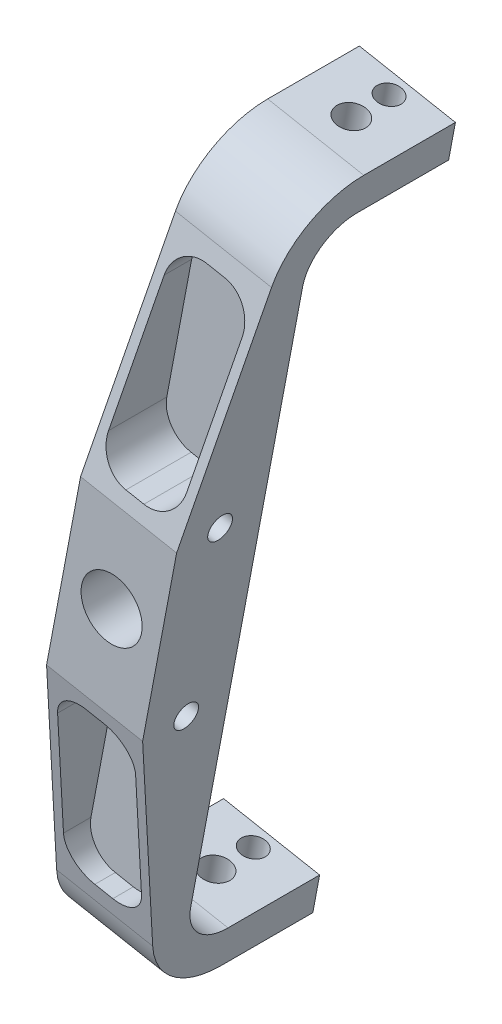
SolidWorks part; units mm, degrees
other "Markup1"
sketch "Sketch6" plane through (39.3536, 123.4271, -45) normal (0.998, 0.0328, -0.0532) x (-0.0595, 0.2351, -0.9701)
other "Markup2"
sketch "Sketch7" plane through (39.3536, 123.4271, -45) normal (0.9999, 0.0057, -0.0131) x (0.0031, -0.9818, -0.1901)
other "Markup4"
sketch "Sketch9" plane through (-39.3536, 123.4271, 27) normal (-0.9915, 0.1233, 0.0413) x (-0.1205, -0.9906, 0.0646)
other "Markup5"
sketch "Sketch12" plane through (-39.3536, 123.4271, 28.5) normal (-0.7749, 0.0474, 0.6304) x (0.632, 0.0395, 0.7739)
material "6061-T6 (SS)"
ref_plane "Front Plane" through (0, 0, 0) normal (0, 0, 1) x (1, 0, 0)
ref_plane "Top Plane" through (0, 0, 0) normal (0, 1, 0) x (1, 0, 0)
ref_plane "Right Plane" through (0, 0, 0) normal (1, 0, 0) x (0, 0, -1)
sketch "Sketch1" plane through (0, 0, 0) normal (0, 0, 1) x (1, 0, 0)
  line L0 (23.3397, 123.7002) -> (23.3397, 145.9252) construction
  line L1 (0, 0) -> (0, -276.86) construction
  line L2 (0, -276.86) -> (-52.2377, -276.86) construction
  line L3 (23.3397, 123.7002) -> (-52.2377, -276.86) construction
  line L8 (-23.3397, -123.7002) -> (-27.4603, -145.5398) construction
  line L9 (-7.6171, -126.6667) -> (39.0622, 120.7336)
  line L14 (-39.0622, -120.7336) -> (7.6171, 126.6667)
  line L17 (23.3397, 123.7002) -> (27.4603, 145.5398) construction
  line L19 (-7.6171, -126.6667) -> (-39.0622, -120.7336)
  line L20 (-23.3397, -123.7002) -> (-25.4, -134.62) construction
  line L21 (7.6171, 126.6667) -> (39.0622, 120.7336)
  line L22 (23.3397, 123.7002) -> (-23.3397, -123.7002) construction
  circle A0 centre (0, 0) radius 276.86 construction
  circle A1 centre (0, 0) radius 10
  circle A2 centre (0, 0) radius 170.5 construction
  point P4 (25.4, 134.62)
  point P6 (0, 0)
  point P10 (0, -170.5)
  point P13 (-10.5081, -129.9032)
  point P17 (0, 0)
  point P18 (41.7595, 124.248)
  point P19 (-41.8145, -123.9803)
  point P20 (10.5081, 129.9032)
  point P25 (-25.4, -134.62)
  point P31 (0, 0)
  point P32 (-23.3397, -123.7002)
  dimension "D4" = 341
  dimension "D9" = 20
  dimension "D2" = 553.72
  dimension "D3" = 22.225
  dimension "D5" = 50.8
  dimension "D6" = 32
  dimension "D7" = 52.2377
  dimension "D8" = 251.7655
  dimension "D11" = 11.1125
  dimension "D12" = 269.24
extrude "Boss-Extrude1" add sketch "Sketch1" along normal blind 28.5
sketch "Sketch2" plane through (0, 0, 0) normal (0, 0, -1) x (-1, 0, 0)
  line L0 (-36.8373, 108.9417) -> (-5.3922, 114.8748)
  line L1 (5.3922, -114.8748) -> (36.8373, -108.9417)
  line L2 (-5.3922, 114.8748) -> (-7.6171, 126.6667)
  line L3 (5.3922, -114.8748) -> (7.6171, -126.6667)
  line L4 (-7.6171, 126.6667) -> (-39.0622, 120.7336)
  line L5 (-39.0622, 120.7336) -> (7.6171, -126.6667)
  line L6 (-7.6171, 126.6667) -> (-39.0622, 120.7336)
  line L7 (39.0622, -120.7336) -> (-7.6171, 126.6667)
  line L9 (-39.0622, 120.7336) -> (-36.8373, 108.9417)
  line L11 (39.0622, -120.7336) -> (36.8373, -108.9417)
  line L14 (7.6171, -126.6667) -> (39.0622, -120.7336)
  line L15 (7.6171, -126.6667) -> (39.0622, -120.7336)
  dimension "D2" = 12
  dimension "D1" = 0
extrude "Boss-Extrude2" add sketch "Sketch2" along normal blind 45
sketch "Sketch4" plane through (-1.6562, 128.4164, 0) normal (0.1854, 0.9827, 0) x (0.9827, -0.1854, 0)
  line L0 (25.4368, -28.5) -> (25.4368, 45) construction
  line L3 (9.4368, 45) -> (41.4368, 45) construction
  line L12 (9.4368, 26.6476) -> (41.4368, 26.6476) construction
  line L13 (9.4368, -28.5) -> (9.4368, 45) construction
  line L14 (41.4368, -28.5) -> (41.4368, 45) construction
  circle A0 centre (25.4368, 26.6476) radius 4.7625
  circle A1 centre (25.4368, 39) radius 3.9688
  point P6 (25.4368, 26.6476)
  dimension "D2" = 9.525
  dimension "D3" = 7.9375
  dimension "D1" = 18.3524
  dimension "D4" = 6
extrude "Cut-Extrude1" cut sketch "Sketch4" against normal through all
fillet "Fillet3" radius 15 2 edges at (21.1148, 111.9082, 0) (-21.1148, -111.9082, 0)
sketch "Sketch10" plane through (-16.0243, 1.3676, 0) normal (0.9827, -0.1854, 0) x (0, 0, -1)
  line L0 (-28.5, 31.6271) -> (-11.3167, 106.5459)
  line L1 (-28.5, 31.6271) -> (-46.9127, 31.4169)
  line L2 (-46.9127, 31.4169) -> (-44.7685, 140.1716)
  line L3 (-44.7685, 140.1716) -> (15, 127.5099)
  line L4 (0, 1.6271) -> (-52.8517, 1.6271) construction
  line L5 (-28.5, 127.5099) -> (45, 127.5099) construction
  line L6 (-28.5, -124.2556) -> (-28.5, 127.5099) construction
  line L7 (-44.7685, -136.9173) -> (15, -124.2556)
  line L8 (-46.9127, -28.1627) -> (-44.7685, -136.9173)
  line L9 (-28.5, -28.3729) -> (-46.9127, -28.1627)
  line L10 (-28.5, -28.3729) -> (-11.3167, -103.2916)
  line L11 (-28.5, 31.6271) -> (0, 31.6271) construction
  line L12 (0, -97.2556) -> (0, 100.5099) construction
  arc A0 (15, 115.5099) -> (0, 100.5099) centre (15, 100.5099) ccw construction
  arc A1 (15, 115.5099) -> (0, 100.5099) centre (15, 100.5099) ccw construction
  arc A2 (15, 127.5099) -> (-11.3167, 106.5459) centre (15, 100.5099) ccw
  arc A3 (15, -112.2556) -> (0, -97.2556) centre (15, -97.2556) cw construction
  arc A4 (15, -124.2556) -> (-11.3167, -103.2916) centre (15, -97.2556) cw
  circle A5 centre (-14.25, 31.6271) radius 4
  circle A6 centre (-14.25, -28.3729) radius 4
  point P14 (15, 127.5099)
  point P29 (15, -124.2556)
  dimension "D1" = 30
  dimension "D2" = 8
extrude "Cut-Extrude2" cut sketch "Sketch10" against normal through all both and the other way through all
sketch "Sketch11" plane through (0, 0, 28.5) normal (0, 0, 1) x (1, 0, 0)
  line L1 (0, 0) -> (75.6649, -14.2764) construction
  line L2 (35.1753, 100.1331) -> (21.2848, 26.5133) construction
  line L3 (35.1753, 100.1331) -> (21.2848, 26.5133) construction
  line L7 (3.5413, 34.9494) -> (9.4373, 33.8369)
  line L12 (-10.1604, 32.4464) -> (3.7302, 106.0662) construction
  line L13 (-10.1604, 32.4464) -> (3.7302, 106.0662) construction
  line L15 (21.118, 41.8095) -> (29.2542, 84.9314)
  line L26 (-4.4312, 46.6301) -> (3.705, 89.752)
  line L27 (2.6111, 100.1348) -> (34.0562, 94.2018) construction
  line L39 (15.3857, 97.7245) -> (21.2816, 96.6121)
  line L40 (-21.2848, -26.5133) -> (-35.1753, -100.1331) construction
  line L41 (-3.7302, -106.0662) -> (10.1604, -32.4464) construction
  line L42 (-21.2816, -96.6121) -> (-15.3857, -97.7245)
  line L43 (-21.118, -41.8095) -> (-29.2542, -84.9314)
  line L44 (4.4312, -46.6301) -> (-3.705, -89.752)
  line L45 (-9.4373, -33.8369) -> (-3.5413, -34.9494)
  arc A0 (9.4373, 33.8369) -> (21.118, 41.8095) centre (11.2913, 43.6636) ccw
  arc A1 (3.5413, 34.9494) -> (-4.4312, 46.6301) centre (5.3954, 44.776) cw
  arc A2 (15.3857, 97.7245) -> (3.705, 89.752) centre (13.5316, 87.8979) ccw
  arc A3 (29.2542, 84.9314) -> (21.2816, 96.6121) centre (19.4275, 86.7855) ccw
  arc A4 (-3.705, -89.752) -> (-15.3857, -97.7245) centre (-13.5316, -87.8979) cw
  arc A5 (-21.2816, -96.6121) -> (-29.2542, -84.9314) centre (-19.4275, -86.7855) cw
  arc A6 (-9.4373, -33.8369) -> (-21.118, -41.8095) centre (-11.2913, -43.6636) ccw
  arc A7 (-3.5413, -34.9494) -> (4.4312, -46.6301) centre (-5.3954, -44.776) cw
  point P12 (-3.4131, 31.3285)
  point P15 (10.5274, 99.16)
  point P16 (29.4323, 95.2747)
  point P17 (15.4917, 27.4432)
  point P18 (27.5728, 26.3797)
  point P19 (-17.6556, 26.3797)
  dimension "D4" = 10
  dimension "D2" = 6
  dimension "D1" = 35
  dimension "D3" = 6
extrude "Cut-Extrude4" cut sketch "Sketch11" against normal offset from surface (22.5 mm away) 6 up to face at (10, 0, 0)
